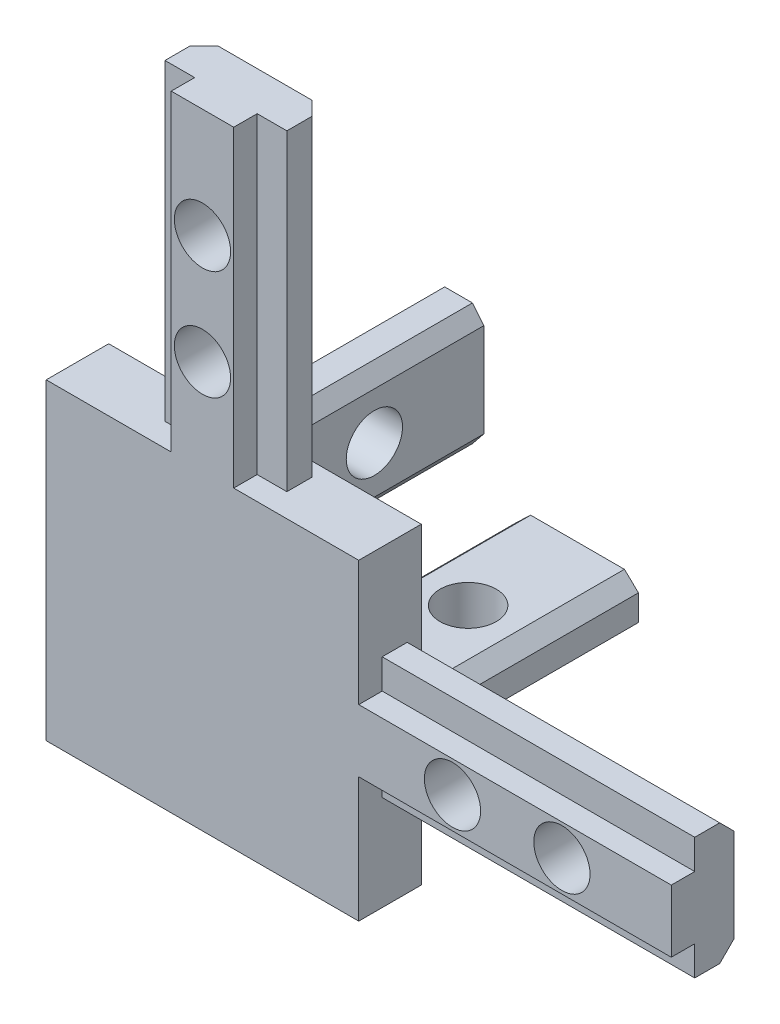
SolidWorks part; units mm, degrees
material "356.0-T6 永久成型铸件 (SS)"
ref_plane "前视基准面" through (0, 0, 0) normal (0, 0, 1) x (1, 0, 0)
ref_plane "上视基准面" through (0, 0, 0) normal (0, 1, 0) x (1, 0, 0)
ref_plane "右视基准面" through (0, 0, 0) normal (1, 0, 0) x (0, 0, -1)
sketch "草图1" plane through (0, 0, 0) normal (0, 0, 1) x (1, 0, 0)
  line L1 (10, -10) -> (-10, -10)
  line L2 (10, -10) -> (10, 10)
  line L3 (10, 10) -> (-10, 10)
  line L4 (-10, -10) -> (-10, 10)
  line L5 (10, -10) -> (-10, 10) construction
  line L6 (10, 10) -> (-10, -10) construction
  point P0 (0, 0)
  dimension "D1" = 20
  dimension "D2" = 20
extrude "凸台-拉伸1" add sketch "草图1" along normal blind 4
sketch "草图2" plane through (0, 0, 0) normal (0, 0, -1) x (-1, 0, 0)
  line L17 (7, -7) -> (7, 7)
  line L18 (-7, -7) -> (7, -7)
  line L19 (-7, 7) -> (-7, -7)
  line L20 (7, 7) -> (-7, 7)
  line L21 (7, -7) -> (7, 7)
  line L22 (-7, -7) -> (7, -7)
  line L23 (-7, 7) -> (-7, -7)
  line L24 (7, 7) -> (-7, 7)
  dimension "D1" = 3
extrude "切除-拉伸1" cut sketch "草图2" against normal blind 2
sketch "草图3" plane through (10, 0, 0) normal (1, 0, 0) x (0, 0, -1)
  line L0 (-4, 0) -> (4.7179, 0) construction
  line L1 (-4, -10) -> (-4, 10) construction
  line L2 (-4, -2) -> (-4, 2)
  line L3 (-4, 2) -> (-2.5, 2)
  line L4 (-2.5, 2) -> (-2.5, 3.9)
  line L5 (-2.5, 3.9) -> (-0.9, 3.9)
  line L6 (-0.9, 3.9) -> (0, 3)
  line L7 (0, -10) -> (0, 10) construction
  line L8 (0, 3) -> (0, -3)
  line L9 (-0.9, -3.9) -> (0, -3)
  line L10 (-2.5, -3.9) -> (-0.9, -3.9)
  line L11 (-2.5, -2) -> (-2.5, -3.9)
  line L12 (-4, -2) -> (-2.5, -2)
  point P14 (0, 0)
  dimension "D1" = 2
  dimension "D2" = 3.9
  dimension "D3" = 1.5
  dimension "D4" = 3
  dimension "D5" = 45
extrude "凸台-拉伸2" add sketch "草图3" along normal blind 20
sketch "草图5" plane through (0, 10, 0) normal (0, 1, 0) x (1, 0, 0)
  line L0 (0, -4) -> (0, 4.7179) construction
  line L1 (2, -4) -> (-2, -4)
  line L2 (-2, -4) -> (-2, -2.5)
  line L3 (-2, -2.5) -> (-3.9, -2.5)
  line L4 (-3.9, -2.5) -> (-3.9, -0.9)
  line L5 (-3.9, -0.9) -> (-3, 0)
  line L6 (-3, 0) -> (3, 0)
  line L7 (3.9, -0.9) -> (3, 0)
  line L8 (3.9, -2.5) -> (3.9, -0.9)
  line L9 (2, -2.5) -> (3.9, -2.5)
  line L10 (2, -4) -> (2, -2.5)
  point P9 (0, 0)
  dimension "D1" = 2
  dimension "D2" = 3.9
  dimension "D3" = 3
extrude "凸台-拉伸3" add sketch "草图5" along normal blind 20
sketch "草图6" plane through (0, 0, 0) normal (0, 0, -1) x (-1, 0, 0)
  line L0 (10, 0) -> (1.1053, 0) construction
  line L1 (10, 2) -> (10, -2)
  line L2 (10, -2) -> (8.5, -2)
  line L3 (8.5, -2) -> (8.5, -3.9)
  line L4 (8.5, -3.9) -> (6.7232, -3.9)
  line L5 (6.7232, -3.9) -> (6, -3)
  line L6 (6, -3) -> (6, 3)
  line L7 (6.7232, 3.9) -> (6, 3)
  line L8 (8.5, 3.9) -> (6.7232, 3.9)
  line L9 (8.5, 2) -> (8.5, 3.9)
  line L10 (10, 2) -> (8.5, 2)
  line L11 (0, -10) -> (0, -1.2354) construction
  line L12 (2, -10) -> (-2, -10)
  line L13 (-2, -10) -> (-2, -8.5)
  line L14 (-2, -8.5) -> (-3.9, -8.5)
  line L15 (-3.9, -8.5) -> (-3.9, -6.8533)
  line L16 (-3.9, -6.8533) -> (-3, -6)
  line L17 (-3, -6) -> (3, -6)
  line L18 (3.9, -6.8533) -> (3, -6)
  line L19 (3.9, -8.5) -> (3.9, -6.8533)
  line L20 (2, -8.5) -> (3.9, -8.5)
  line L21 (2, -10) -> (2, -8.5)
  line L22 (10, 10) -> (10, -10) construction
  line L23 (10, -10) -> (-10, -10) construction
  point P9 (6, 0)
  point P22 (0, -6)
  dimension "D1" = 2
  dimension "D2" = 3.9
  dimension "D3" = 3
  dimension "D4" = 2
  dimension "D5" = 3.9
  dimension "D6" = 3
  dimension "D7" = 1.5
  dimension "D8" = 2.5
  dimension "D9" = 1.5
  dimension "D10" = 2.5
extrude "凸台-拉伸4" add sketch "草图6" along normal blind 20 and the other way blind 4
sketch "草图7" plane through (-10, 0, 0) normal (-1, 0, 0) x (0, 0, 1)
  circle A0 centre (-6, 0) radius 1.8
  circle A1 centre (-13, 0) radius 1.8
  dimension "D2" = 3.6
  dimension "D1" = 6
  dimension "D3" = 2
extrude "切除-拉伸5" cut sketch "草图7" against normal through all contours A0 | A1
sketch "草图8" plane through (0, 0, 0) normal (0, 0, -1) x (-1, 0, 0)
  line L0 (-10, 3) -> (-10, 10) construction
  line L1 (-10, 10) -> (-3, 10) construction
  circle A0 centre (-16, 0) radius 1.8
  circle A1 centre (0, 16) radius 1.8
  circle A2 centre (0, 23) radius 1.8
  circle A3 centre (-23, 0) radius 1.8
  dimension "D1" = 3.6
  dimension "D2" = 3.6
  dimension "D3" = 6
  dimension "D4" = 6
  dimension "D5" = 2
  dimension "D6" = 2
extrude "切除-拉伸6" cut sketch "草图8" against normal blind 20
sketch "草图9" plane through (0, -10, 0) normal (0, -1, 0) x (1, 0, 0)
  circle A0 centre (0, -6) radius 1.8
  circle A1 centre (0, -13) radius 1.8
  dimension "D1" = 3.6
  dimension "D2" = 6
  dimension "D3" = 2
extrude "切除-拉伸7" cut sketch "草图9" against normal blind 20
